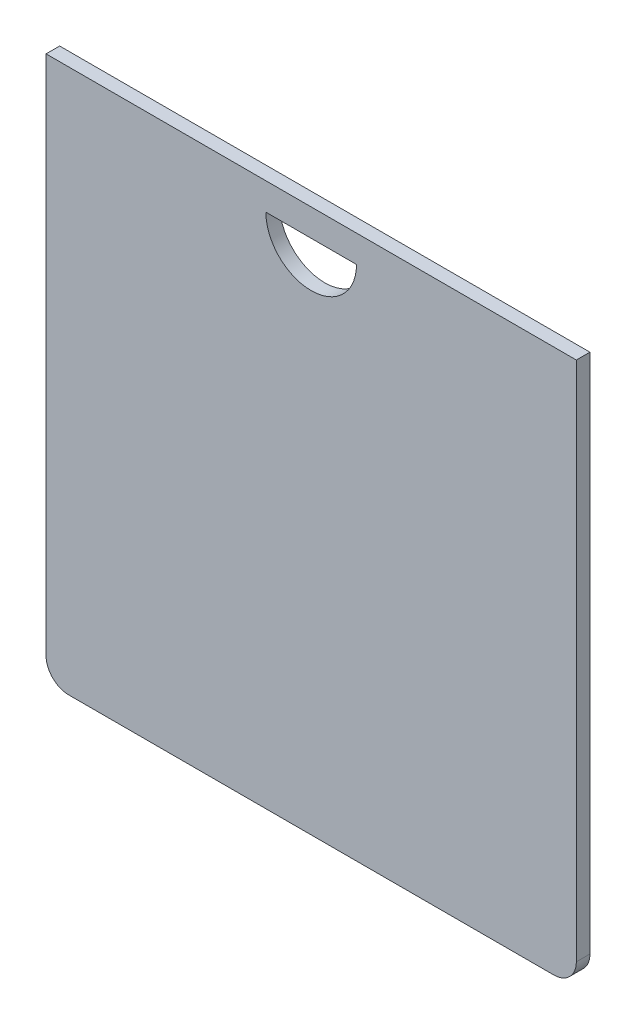
SolidWorks part; units mm, degrees
material "ABS"
ref_plane "Спереди" through (0, 0, 0) normal (0, 0, 1) x (1, 0, 0)
ref_plane "Сверху" through (0, 0, 0) normal (0, 1, 0) x (1, 0, 0)
ref_plane "Справа" through (0, 0, 0) normal (1, 0, 0) x (0, 0, -1)
sketch "Эскиз1" plane through (0, 0, 0) normal (0, 0, 1) x (1, 0, 0)
  line L1 (0, 60) -> (58.5, 60)
  line L2 (0, 60) -> (0, 0)
  line L3 (0, 0) -> (58.5, 0)
  line L4 (58.5, 60) -> (58.5, 0)
  dimension "D1" = 60
  dimension "D2" = 58.5
extrude "Бобышка-Вытянуть1" add sketch "Эскиз1" along normal blind 1.5
fillet "Скругление1" radius 2.5 2 edges at (58.5, 0, 0.75) (0, 0, 0.75)
sketch "Эскиз2" plane through (0, 0, 1.5) normal (0, 0, 1) x (1, 0, 0)
  line L0 (24.25, 57) -> (34.25, 57)
  line L1 (58.5, 60) -> (0, 60) construction
  arc A0 (24.25, 57) -> (34.25, 57) centre (29.25, 57) ccw
  point P7 (29.25, 60)
  dimension "D2" = 5
  dimension "D1" = 3
extrude "Вырез-Вытянуть1" cut sketch "Эскиз2" against normal through all
